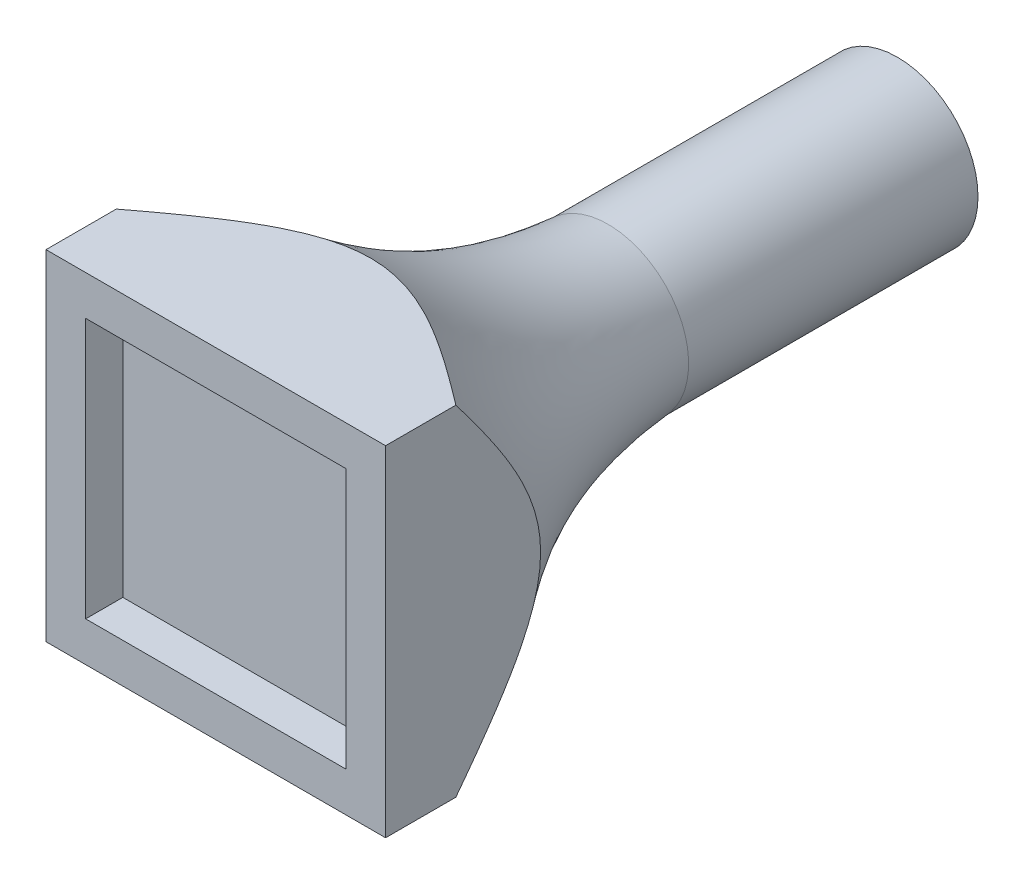
SolidWorks part; units mm, degrees
ref_plane "Front Plane" through (0, 0, 0) normal (0, 0, 1) x (1, 0, 0)
ref_plane "Top Plane" through (0, 0, 0) normal (0, 1, 0) x (1, 0, 0)
ref_plane "Right Plane" through (0, 0, 0) normal (1, 0, 0) x (0, 0, -1)
sketch "Sketch1" plane through (0, 0, 0) normal (0, 0, 1) x (1, 0, 0)
  circle A0 centre (0, 0) radius 6.5
  dimension "D1" = 13
extrude "Boss-Extrude1" add sketch "Sketch1" along normal blind 50
sketch "Sketch2" plane through (0, 0, 50) normal (0, 0, 1) x (1, 0, 0)
  line L0 (13.7, 13.7) -> (-13.7, 13.7)
  line L1 (10.5, 10.5) -> (-10.5, 10.5) construction
  line L2 (10.5, 10.5) -> (10.5, -10.5) construction
  line L3 (10.5, -10.5) -> (-10.5, -10.5) construction
  line L4 (-10.5, 10.5) -> (-10.5, -10.5) construction
  line L5 (10.5, 10.5) -> (-10.5, -10.5) construction
  line L6 (10.5, -10.5) -> (-10.5, 10.5) construction
  line L7 (-13.7, 13.7) -> (-13.7, -13.7)
  line L8 (13.7, -13.7) -> (-13.7, -13.7)
  line L9 (13.7, 13.7) -> (13.7, -13.7)
  point P0 (0, 0)
  dimension "D1" = 21
  dimension "D2" = 21
  dimension "D3" = 3.2
extrude "Boss-Extrude2" add sketch "Sketch2" along normal blind 5
sketch "Sketch3" plane through (0, 0, 55) normal (0, 0, 1) x (1, 0, 0)
  line L1 (10.5, 10.5) -> (-10.5, 10.5)
  line L2 (10.5, 10.5) -> (10.5, -10.5)
  line L3 (10.5, -10.5) -> (-10.5, -10.5)
  line L4 (-10.5, 10.5) -> (-10.5, -10.5)
  line L5 (10.5, 10.5) -> (-10.5, -10.5) construction
  line L6 (10.5, -10.5) -> (-10.5, 10.5) construction
  point P0 (0, 0)
  dimension "D1" = 21
  dimension "D2" = 21
extrude "Cut-Extrude1" cut sketch "Sketch3" against normal blind 3
sketch "Sketch5" plane through (0, 0, 0) normal (1, 0, 0) x (0, 0, -1)
  line L0 (-63.5412, 0) -> (-78.0067, 0)
sketch "Sketch6" plane through (0, 0, 0) normal (1, 0, 0) x (0, 0, -1)
  line L0 (-50, 0) -> (-50, 20)
  line L1 (-50, -13.7) -> (-50, 13.7) construction
  line L2 (-50, 0) -> (0, 0)
  line L3 (0, 0) -> (0, 6.5)
  line L4 (18.8276, 6.5) -> (-18.8276, 6.5) construction
  spline S0 degree 3 poles (-50, 20) (-32.3301, 3.3145) (-23.5345, 6.5) (0, 6.5) knots 0 0 0 0 1 1 1 1
  dimension "D1" = 20
revolve "Revolve1" add sketch "Sketch6" angle 360 about L0
sketch "Sketch7" plane through (0, 0, 50) normal (0, 0, 1) x (1, 0, 0)
  line L1 (13.7, 13.7) -> (-13.7, 13.7)
  line L2 (13.7, 13.7) -> (13.7, -13.7)
  line L3 (13.7, -13.7) -> (-13.7, -13.7)
  line L4 (-13.7, 13.7) -> (-13.7, -13.7)
  line L5 (13.7, 13.7) -> (-13.7, -13.7) construction
  line L6 (13.7, -13.7) -> (-13.7, 13.7) construction
  line L7 (23.5697, 23.5697) -> (-23.5697, 23.5697)
  line L8 (23.5697, 23.5697) -> (23.5697, -23.5697)
  line L9 (23.5697, -23.5697) -> (-23.5697, -23.5697)
  line L10 (-23.5697, 23.5697) -> (-23.5697, -23.5697)
  line L11 (23.5697, 23.5697) -> (-23.5697, -23.5697) construction
  line L12 (23.5697, -23.5697) -> (-23.5697, 23.5697) construction
  point P0 (0, 0)
  point P7 (0, 0)
extrude "Cut-Extrude2" cut sketch "Sketch7" against normal blind 78
sketch "Sketch8" plane through (0, 0, 0) normal (0, 0, -1) x (-1, 0, 0)
  circle A0 centre (0, 0) radius 2.15
  dimension "D1" = 4.3
extrude "Cut-Extrude3" cut sketch "Sketch8" against normal blind 25
sketch "Sketch9" plane through (0, 0, 25) normal (0, 0, -1) x (-1, 0, 0)
  line L1 (4.1569, 0) -> (2.0785, 3.6)
  line L2 (2.0785, 3.6) -> (-2.0785, 3.6)
  line L3 (-2.0785, 3.6) -> (-4.1569, 0)
  line L4 (-4.1569, 0) -> (-2.0785, -3.6)
  line L5 (-2.0785, -3.6) -> (2.0785, -3.6)
  line L6 (2.0785, -3.6) -> (4.1569, 0)
  circle A0 centre (0, 0) radius 3.6 construction
  dimension "D1" = 7.2
extrude "Cut-Extrude4" cut sketch "Sketch9" against normal blind 3.5
sketch "Sketch10" plane through (0, 0, 28.5) normal (0, 0, -1) x (-1, 0, 0)
  circle A0 centre (0, 0) radius 2.15
extrude "Cut-Extrude5" cut sketch "Sketch10" against normal blind 15
